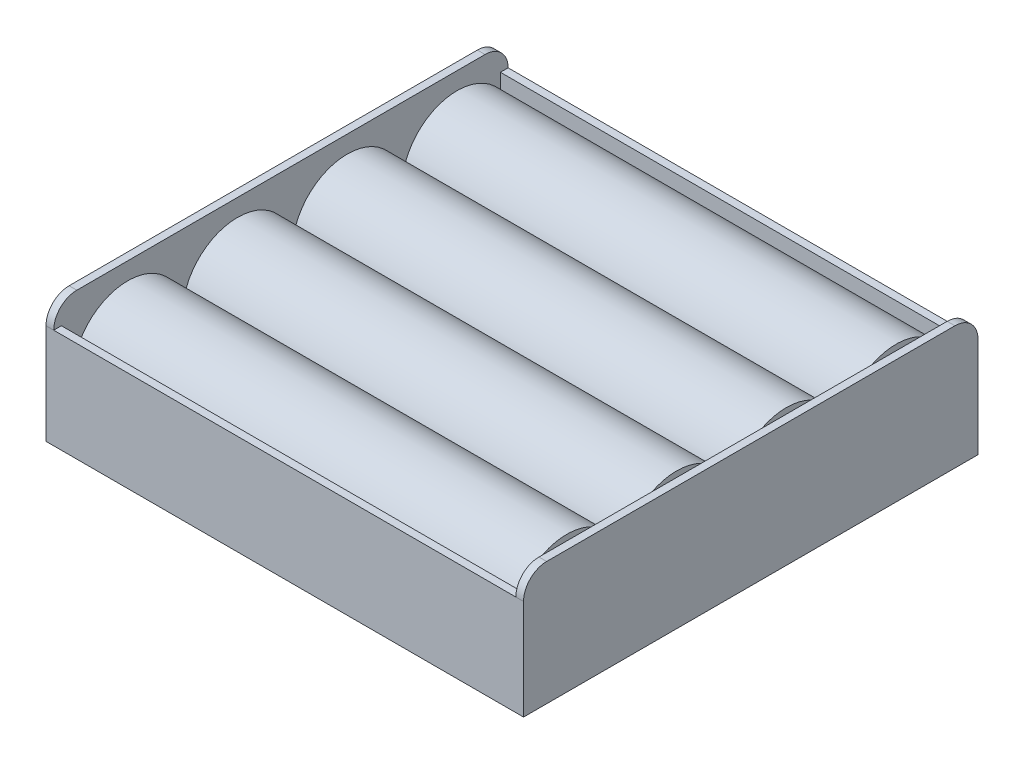
SolidWorks part; units mm, degrees
ref_plane "Ebene vorne" through (0, 0, 0) normal (0, 0, 1) x (1, 0, 0)
ref_plane "Ebene oben" through (0, 0, 0) normal (0, 1, 0) x (1, 0, 0)
ref_plane "Ebene rechts" through (0, 0, 0) normal (1, 0, 0) x (0, 0, -1)
sketch "Skizze1" plane through (0, 0, 0) normal (1, 0, 0) x (0, 0, -1)
  line L0 (29.5, 13) -> (29.5, 0)
  line L1 (-29.5, 0) -> (29.5, 0)
  line L2 (0, 0) -> (0, 1) construction
  line L3 (28.5, 1) -> (-28.5, 1)
  line L4 (-28.5, 1) -> (-28.5, 13)
  line L5 (-28.5, 13) -> (-29.5, 13)
  line L6 (-29.5, 13) -> (-29.5, 0)
  line L7 (28.5, 13) -> (29.5, 13)
  line L8 (28.5, 1) -> (28.5, 13)
  dimension "D1" = 29.5
  dimension "D2" = 13
  dimension "D3" = 1
extrude "Linear austragen1" add sketch "Skizze1" along normal blind 30
sketch "Skizze2" plane through (30, 0, 0) normal (1, 0, 0) x (0, 0, -1)
  line L0 (-29.5, 0) -> (29.5, 0)
  line L1 (0, 0) -> (0, 16) construction
  line L2 (26.5, 16) -> (-26.5, 16)
  line L3 (-29.5, 0) -> (-29.5, 13)
  line L4 (29.5, 0) -> (29.5, 13)
  arc A0 (-29.5, 13) -> (-26.5, 16) centre (-26.5, 13) cw
  arc A1 (29.5, 13) -> (26.5, 16) centre (26.5, 13) ccw
  dimension "D1" = 16
extrude "Linear austragen2" add sketch "Skizze2" along normal blind 1
sketch "Skizze3" plane through (0, 0, 0) normal (1, 0, 0) x (0, 0, -1)
  line L1 (-28.5, 1) -> (-28.5, 13) construction
  line L2 (28.5, 1) -> (-28.5, 1) construction
  line L3 (-21.375, 8.125) -> (21.375, 8.125) construction
  line L4 (28.5, 13) -> (28.5, 1) construction
  circle A0 centre (-21.375, 8.125) radius 7.125
  circle A1 centre (-7.125, 8.125) radius 7.125
  circle A2 centre (7.125, 8.125) radius 7.125
  circle A3 centre (21.375, 8.125) radius 7.125
extrude "Linear austragen3" add sketch "Skizze3" along normal mid plane 57 separate body
mirror "Spiegeln11" about plane through (0, 13, -29.5) normal (-1, 0, 0) of "Linear austragen2", "Linear austragen1"
